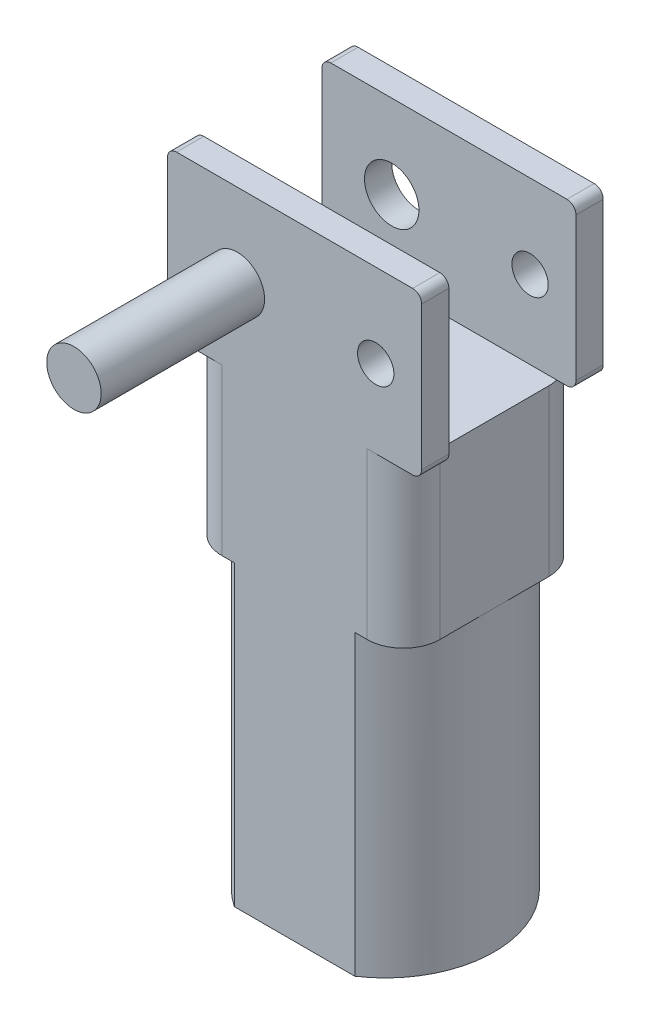
SolidWorks part; units mm, degrees
ref_plane "Front Plane" through (0, 0, 0) normal (0, 0, 1) x (1, 0, 0)
ref_plane "Top Plane" through (0, 0, 0) normal (0, 1, 0) x (1, 0, 0)
ref_plane "Right Plane" through (0, 0, 0) normal (1, 0, 0) x (0, 0, -1)
sketch "Sketch1" plane through (0, 0, 0) normal (0, 1, 0) x (1, 0, 0)
  line L0 (-11.5221, 0) -> (17.4901, 0) construction
  line L1 (-3.3166, 5) -> (3.3166, 5)
  line L2 (-3.3166, -5) -> (3.3166, -5)
  arc A0 (-3.3166, 5) -> (-3.3166, -5) centre (0, 0) ccw
  arc A1 (3.3166, -5) -> (3.3166, 5) centre (0, 0) ccw
  dimension "D1" = 12
  dimension "D2" = 10
extrude "Boss-Extrude1" add sketch "Sketch1" along normal blind 16.4
sketch "Sketch2" plane through (0, 16.4, 0) normal (0, 1, 0) x (1, 0, 0)
  line L5 (3.3166, 5) -> (-3.3166, 5) construction
  line L6 (-6, 5) -> (6, 5)
  line L7 (-6, 5) -> (-6, -5)
  line L8 (-6, -5) -> (6, -5)
  line L9 (6, 5) -> (6, -5)
  line L10 (-3.3166, -5) -> (3.3166, -5) construction
  line L11 (0, 7.4022) -> (0, -8.7453) construction
  dimension "D1" = 12
extrude "Boss-Extrude2" add sketch "Sketch2" along normal blind 9.1
fillet "Fillet1" radius 2 4 edges at (-6, 20.95, -5) (-6, 20.95, 5) (6, 20.95, -5) (6, 20.95, 5)
sketch "Sketch3" plane through (0, 0, 5) normal (0, 0, 1) x (1, 0, 0)
  line L0 (-4, 25.5) -> (4, 25.5) construction
  line L1 (-7, 34.4) -> (7, 34.4)
  line L2 (-7, 34.4) -> (-7, 25.5)
  line L3 (-7, 25.5) -> (7, 25.5)
  line L4 (7, 34.4) -> (7, 25.5)
  line L5 (0, 34.3709) -> (0, -6.3709) construction
  line L6 (-3.15, 29.8) -> (15.7285, 29.8) construction
  circle A0 centre (-3.15, 29.8) radius 1.5
  circle A1 centre (4.47, 29.8) radius 1
  dimension "D3" = 3
  dimension "D6" = 2
  dimension "D1" = 14
  dimension "D2" = 8.9
  dimension "D4" = 4.3
  dimension "D5" = 3.85
  dimension "D7" = 7.62
extrude "Boss-Extrude3" add sketch "Sketch3" against normal blind 1.5
fillet "Fillet2" radius 0.5 4 edges at (7, 25.5, 4.25) (-7, 25.5, 4.25) (-7, 34.4, 4.25) (7, 34.4, 4.25)
mirror "Mirror1" about plane through (0, 0, 0) normal (0, 0, 1) of "Fillet2", "Boss-Extrude3"
sketch "Sketch4" plane through (0, 0, 5) normal (0, 0, 1) x (1, 0, 0)
  circle A0 centre (-3.15, 29.8) radius 1.5 construction
  circle A1 centre (-3.15, 29.8) radius 1.5
extrude "Boss-Extrude4" add sketch "Sketch4" along normal blind 9 separate body
